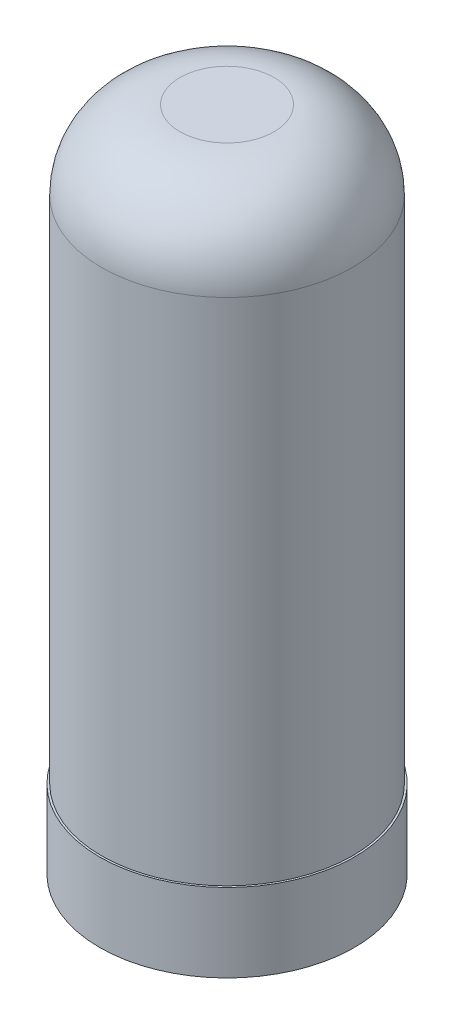
SolidWorks part; units mm, degrees
ref_plane "Front Plane" through (0, 0, 0) normal (0, 0, 1) x (1, 0, 0)
ref_plane "Top Plane" through (0, 0, 0) normal (0, 1, 0) x (1, 0, 0)
ref_plane "Right Plane" through (0, 0, 0) normal (1, 0, 0) x (0, 0, -1)
sketch "Esquisse1" plane through (0, 0, 0) normal (0, 1, 0) x (1, 0, 0)
  circle A0 centre (0, 0) radius 32.5
  circle A1 centre (0, 0) radius 3.25
  dimension "D1" = 65
  dimension "D2" = 6.5
extrude "Boss.-Extru.1" add sketch "Esquisse1" along normal blind 20
sketch "Esquisse2" plane through (0, 20, 0) normal (0, 1, 0) x (1, 0, 0)
  circle A0 centre (0, 0) radius 32
  dimension "D1" = 64
extrude "Boss.-Extru.2" add sketch "Esquisse2" along normal blind 150
fillet "Congé1" radius 20 1 edges at (0, 170, 32)
